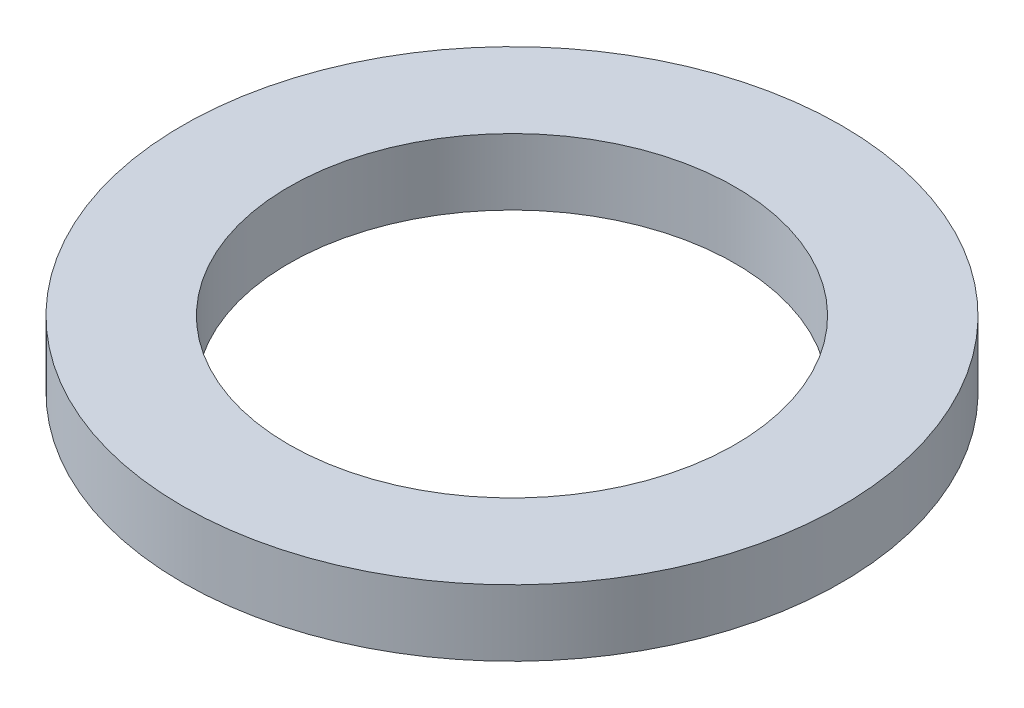
SolidWorks part; units mm, degrees
ref_plane "Front Plane" through (0, 0, 0) normal (0, 0, 1) x (1, 0, 0)
ref_plane "Top Plane" through (0, 0, 0) normal (0, 1, 0) x (1, 0, 0)
ref_plane "Right Plane" through (0, 0, 0) normal (1, 0, 0) x (0, 0, -1)
sketch "Sketch1" plane through (0, 0, 0) normal (0, 1, 0) x (1, 0, 0)
  circle A0 centre (0, 0) radius 40.535
  circle A1 centre (0, 0) radius 27.45
  dimension "D1" = 81.07
  dimension "D2" = 54.9
extrude "Boss-Extrude1" add sketch "Sketch1" along normal blind 8.15
